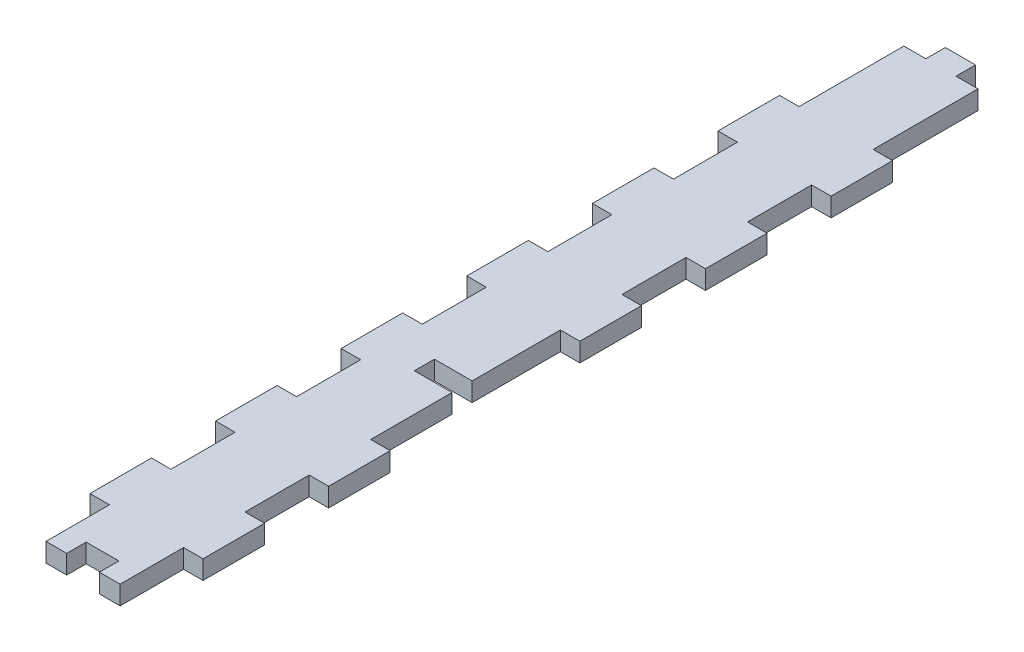
SolidWorks part; units mm, degrees
ref_plane "Front Plane" through (0, 0, 0) normal (0, 0, 1) x (1, 0, 0)
ref_plane "Top Plane" through (0, 0, 0) normal (0, 1, 0) x (1, 0, 0)
ref_plane "Right Plane" through (0, 0, 0) normal (1, 0, 0) x (0, 0, -1)
sketch "Sketch1" plane through (0, 0, 0) normal (0, 1, 0) x (1, 0, 0)
  line L0 (0, 0) -> (0, -139.6944) construction
  line L1 (-9, 0) -> (9, 0)
  line L2 (-9, 0) -> (-9, -139.6944)
  line L3 (-9, -139.6944) -> (9, -139.6944)
  line L4 (9, 0) -> (9, -139.6944)
extrude "Boss-Extrude1" add sketch "Sketch1" against normal up to vertex (3 mm away)
sketch "Sketch2" plane through (0, 0, 0) normal (0, 1, 0) x (1, 0, 0)
  line L0 (6, -3) -> (6, -139.6944) construction
  line L1 (-6, -139.6944) -> (-6, -3) construction
  line L2 (6, -3) -> (-6, -3) construction
  line L3 (-6, -3) -> (-6, 0) construction
  line L4 (9, 0) -> (-9, 0)
  line L5 (9, -139.6944) -> (9, 0)
  line L6 (-9, -139.6944) -> (9, -139.6944)
  line L7 (-9, 0) -> (-9, -139.6944)
  line L8 (9, 0) -> (-9, 0) construction
  line L9 (9, -139.6944) -> (9, 0) construction
  line L10 (-9, -139.6944) -> (9, -139.6944) construction
  line L11 (-9, 0) -> (-9, -139.6944) construction
  line L12 (-6, -3) -> (-9, -3) construction
  line L13 (2.5, 0) -> (9, 0)
  line L14 (9, -39.6944) -> (6, -39.6944)
  line L15 (2.5, -3) -> (2.5, 0)
  line L17 (0, 0) -> (0, -139.6944) construction
  line L18 (9, -49.6944) -> (6, -49.6944)
  line L20 (9, 0) -> (9, -19.6944)
  line L21 (9, -29.6944) -> (6, -29.6944)
  line L22 (6, -19.6944) -> (6, -3)
  line L23 (6, -3) -> (2.5, -3)
  line L24 (9, -19.6944) -> (6, -19.6944)
  line L25 (9, -59.6944) -> (6, -59.6944)
  line L27 (9, -69.6944) -> (6, -69.6944)
  line L29 (9, -79.6944) -> (6, -79.6944) construction
  line L31 (9, -109.6944) -> (6, -109.6944)
  line L33 (9, -119.6944) -> (6, -119.6944)
  line L35 (9, -129.6944) -> (6, -129.6944)
  line L37 (-9, -119.6944) -> (-6, -119.6944)
  line L39 (-9, -129.6944) -> (-6, -129.6944)
  line L41 (-9, -79.6944) -> (-6, -79.6944)
  line L42 (-9, -89.6944) -> (-9, -99.6944)
  line L43 (-9, -109.6944) -> (-6, -109.6944)
  line L44 (-6, -89.6944) -> (-6, -99.6944)
  line L45 (-9, -59.6944) -> (-6, -59.6944)
  line L47 (-9, -69.6944) -> (-6, -69.6944)
  line L49 (-9, -39.6944) -> (-6, -39.6944)
  line L51 (-9, -49.6944) -> (-6, -49.6944)
  line L53 (-9, -29.6944) -> (-6, -29.6944)
  line L54 (-9, 0) -> (-9, -19.6944)
  line L55 (-2.5, 0) -> (-9, 0)
  line L56 (-2.5, -3) -> (-2.5, 0)
  line L57 (-6, -3) -> (-2.5, -3)
  line L58 (-6, -19.6944) -> (-6, -3)
  line L59 (9, -89.6944) -> (6, -89.6944) construction
  line L60 (9, -99.6944) -> (6, -99.6944)
  line L61 (9, -136.6944) -> (-9, -136.6944) construction
  line L62 (-6, -19.6944) -> (-9, -19.6944)
  line L67 (2.5, -136.6944) -> (-2.5, -136.6944)
  line L68 (2.5, -136.6944) -> (2.5, -139.6944)
  line L69 (2.5, -139.6944) -> (-2.5, -139.6944)
  line L70 (-2.5, -136.6944) -> (-2.5, -139.6944)
  line L71 (9, -29.6944) -> (9, -39.6944)
  line L72 (6, -29.6944) -> (6, -39.6944)
  line L73 (-6, -29.6944) -> (-6, -39.6944)
  line L74 (-9, -29.6944) -> (-9, -39.6944)
  line L75 (9, -49.6944) -> (9, -59.6944)
  line L76 (6, -49.6944) -> (6, -59.6944)
  line L77 (-6, -49.6944) -> (-6, -59.6944)
  line L78 (-9, -49.6944) -> (-9, -59.6944)
  line L79 (-6, -99.6944) -> (-9, -99.6944)
  line L80 (-6, -89.6944) -> (-9, -89.6944)
  line L81 (9, -69.6944) -> (9, -99.6944)
  line L82 (6, -69.6944) -> (6, -83.7444)
  line L83 (-6, -69.6944) -> (-6, -79.6944)
  line L84 (-9, -69.6944) -> (-9, -79.6944)
  line L85 (6, -86.7444) -> (6, -99.6944)
  line L86 (9, -109.6944) -> (9, -119.6944)
  line L87 (6, -109.6944) -> (6, -119.6944)
  line L88 (-6, -109.6944) -> (-6, -119.6944)
  line L89 (-9, -109.6944) -> (-9, -119.6944)
  line L90 (-6, -129.6944) -> (-6, -139.6944)
  line L91 (-6, -139.6944) -> (-9, -139.6944)
  line L92 (-9, -139.6944) -> (-9, -129.6944)
  line L93 (6, -129.6944) -> (6, -139.6944)
  line L94 (6, -139.6944) -> (9, -139.6944)
  line L95 (9, -139.6944) -> (9, -129.6944)
  line L96 (-9, -83.7444) -> (9, -83.7444) construction
  line L97 (9, -86.7444) -> (-9, -86.7444) construction
  line L99 (6, -83.7444) -> (0, -83.7444)
  line L101 (6, -86.7444) -> (0, -86.7444)
  line L102 (0, -83.7444) -> (0, -86.7444)
  dimension "D1" = 0
sketch "Sketch4" plane through (0, 0, 0) normal (0, 1, 0) x (1, 0, 0)
  line L0 (5.9, -19.7944) -> (9.1, -19.7944)
  line L1 (9.1, -19.7944) -> (9.1, 0.1)
  line L2 (9.1, 0.1) -> (2.4, 0.1)
  line L3 (2.4, 0.1) -> (2.4, -3.1)
  line L4 (9, -49.6944) -> (6, -49.6944)
  line L5 (6, -49.6944) -> (6, -59.6944)
  line L6 (6, -19.6944) -> (9, -19.6944)
  line L7 (9, -19.6944) -> (9, 0)
  line L8 (9, 0) -> (2.5, 0)
  line L9 (2.5, 0) -> (2.5, -3)
  line L10 (2.5, -3) -> (6, -3)
  line L11 (6, -3) -> (6, -19.6944)
  line L12 (6, -19.6944) -> (9, -19.6944) construction
  line L13 (9, -19.6944) -> (9, 0) construction
  line L14 (9, 0) -> (2.5, 0) construction
  line L15 (2.5, 0) -> (2.5, -3) construction
  line L16 (2.5, -3) -> (6, -3) construction
  line L17 (6, -3) -> (6, -19.6944) construction
  line L18 (6, -59.6944) -> (9, -59.6944)
  line L19 (9, -59.6944) -> (9, -49.6944)
  line L20 (9, -49.6944) -> (6, -49.6944) construction
  line L21 (6, -49.6944) -> (6, -59.6944) construction
  line L22 (6, -59.6944) -> (9, -59.6944) construction
  line L23 (9, -59.6944) -> (9, -49.6944) construction
  line L24 (6, -39.6944) -> (9, -39.6944)
  line L25 (6, -29.6944) -> (6, -39.6944)
  line L26 (9, -29.6944) -> (6, -29.6944)
  line L27 (9, -39.6944) -> (9, -29.6944)
  line L28 (6, -39.6944) -> (9, -39.6944) construction
  line L29 (6, -29.6944) -> (6, -39.6944) construction
  line L30 (9, -29.6944) -> (6, -29.6944) construction
  line L31 (9, -39.6944) -> (9, -29.6944) construction
  line L32 (9, -129.6944) -> (6, -129.6944)
  line L33 (6, -129.6944) -> (6, -139.6944)
  line L34 (6, -139.6944) -> (9, -139.6944)
  line L35 (9, -139.6944) -> (9, -129.6944)
  line L36 (9, -129.6944) -> (6, -129.6944) construction
  line L37 (6, -129.6944) -> (6, -139.6944) construction
  line L38 (6, -139.6944) -> (9, -139.6944) construction
  line L39 (9, -139.6944) -> (9, -129.6944) construction
  line L40 (9, -109.6944) -> (6, -109.6944)
  line L41 (6, -109.6944) -> (6, -119.6944)
  line L42 (6, -119.6944) -> (9, -119.6944)
  line L43 (9, -119.6944) -> (9, -109.6944)
  line L44 (9, -109.6944) -> (6, -109.6944) construction
  line L45 (6, -109.6944) -> (6, -119.6944) construction
  line L46 (6, -119.6944) -> (9, -119.6944) construction
  line L47 (9, -119.6944) -> (9, -109.6944) construction
  line L48 (-9, -59.6944) -> (-6, -59.6944)
  line L49 (-6, -59.6944) -> (-6, -49.6944)
  line L50 (-6, -49.6944) -> (-9, -49.6944)
  line L51 (-9, -49.6944) -> (-9, -59.6944)
  line L52 (-9, -59.6944) -> (-6, -59.6944) construction
  line L53 (-6, -59.6944) -> (-6, -49.6944) construction
  line L54 (-6, -49.6944) -> (-9, -49.6944) construction
  line L55 (-9, -49.6944) -> (-9, -59.6944) construction
  line L56 (-6, -109.6944) -> (-9, -109.6944)
  line L57 (-6, -119.6944) -> (-6, -109.6944)
  line L58 (-9, -119.6944) -> (-6, -119.6944)
  line L59 (-9, -109.6944) -> (-9, -119.6944)
  line L60 (-6, -109.6944) -> (-9, -109.6944) construction
  line L61 (-6, -119.6944) -> (-6, -109.6944) construction
  line L62 (-9, -119.6944) -> (-6, -119.6944) construction
  line L63 (-9, -109.6944) -> (-9, -119.6944) construction
  line L64 (-9, -79.6944) -> (-6, -79.6944)
  line L65 (-6, -79.6944) -> (-6, -69.6944)
  line L66 (-6, -69.6944) -> (-9, -69.6944)
  line L67 (-9, -69.6944) -> (-9, -79.6944)
  line L68 (-9, -79.6944) -> (-6, -79.6944) construction
  line L69 (-6, -79.6944) -> (-6, -69.6944) construction
  line L70 (-6, -69.6944) -> (-9, -69.6944) construction
  line L71 (-9, -69.6944) -> (-9, -79.6944) construction
  line L72 (-6, -129.6944) -> (-9, -129.6944)
  line L73 (-6, -139.6944) -> (-6, -129.6944)
  line L74 (-9, -139.6944) -> (-6, -139.6944)
  line L75 (-9, -129.6944) -> (-9, -139.6944)
  line L76 (-6, -129.6944) -> (-9, -129.6944) construction
  line L77 (-6, -139.6944) -> (-6, -129.6944) construction
  line L78 (-9, -139.6944) -> (-6, -139.6944) construction
  line L79 (-9, -129.6944) -> (-9, -139.6944) construction
  line L80 (-6, -39.6944) -> (-6, -29.6944)
  line L81 (-9, -39.6944) -> (-6, -39.6944)
  line L82 (-9, -29.6944) -> (-9, -39.6944)
  line L83 (-6, -29.6944) -> (-9, -29.6944)
  line L84 (-6, -39.6944) -> (-6, -29.6944) construction
  line L85 (-9, -39.6944) -> (-6, -39.6944) construction
  line L86 (-9, -29.6944) -> (-9, -39.6944) construction
  line L87 (-6, -29.6944) -> (-9, -29.6944) construction
  line L88 (-9, -89.6944) -> (-9, -99.6944)
  line L89 (-9, -99.6944) -> (-6, -99.6944)
  line L90 (-6, -99.6944) -> (-6, -89.6944)
  line L91 (-6, -89.6944) -> (-9, -89.6944)
  line L92 (-9, -89.6944) -> (-9, -99.6944) construction
  line L93 (-9, -99.6944) -> (-6, -99.6944) construction
  line L94 (-6, -99.6944) -> (-6, -89.6944) construction
  line L95 (-6, -89.6944) -> (-9, -89.6944) construction
  line L96 (2.5, -136.6944) -> (-2.5, -136.6944)
  line L97 (-2.5, -136.6944) -> (-2.5, -139.6944)
  line L98 (-2.5, -139.6944) -> (2.5, -139.6944)
  line L99 (2.5, -139.6944) -> (2.5, -136.6944)
  line L100 (6, -83.7444) -> (0, -83.7444)
  line L101 (6, -69.6944) -> (6, -83.7444)
  line L102 (9, -69.6944) -> (6, -69.6944)
  line L103 (9, -99.6944) -> (9, -69.6944)
  line L104 (6, -99.6944) -> (9, -99.6944)
  line L105 (6, -86.7444) -> (6, -99.6944)
  line L106 (0, -86.7444) -> (6, -86.7444)
  line L107 (0, -83.7444) -> (0, -86.7444)
  line L108 (6, -83.7444) -> (0, -83.7444) construction
  line L109 (6, -69.6944) -> (6, -83.7444) construction
  line L110 (9, -69.6944) -> (6, -69.6944) construction
  line L111 (9, -99.6944) -> (9, -69.6944) construction
  line L112 (6, -99.6944) -> (9, -99.6944) construction
  line L113 (6, -86.7444) -> (6, -99.6944) construction
  line L114 (0, -86.7444) -> (6, -86.7444) construction
  line L115 (0, -83.7444) -> (0, -86.7444) construction
  line L116 (2.5, -136.6944) -> (-2.5, -136.6944) construction
  line L117 (-2.5, -136.6944) -> (-2.5, -139.6944) construction
  line L118 (-2.5, -139.6944) -> (2.5, -139.6944) construction
  line L119 (2.5, -139.6944) -> (2.5, -136.6944) construction
  line L120 (2.4, -3.1) -> (5.9, -3.1)
  line L121 (5.9, -3.1) -> (5.9, -19.7944)
  line L122 (-9, 0) -> (-9, -19.6944)
  line L123 (-2.5, 0) -> (-9, 0)
  line L124 (-2.5, -3) -> (-2.5, 0)
  line L125 (-6, -3) -> (-2.5, -3)
  line L126 (-6, -19.6944) -> (-6, -3)
  line L127 (-9, -19.6944) -> (-6, -19.6944)
  line L128 (-9, 0) -> (-9, -19.6944) construction
  line L129 (-2.5, 0) -> (-9, 0) construction
  line L130 (-2.5, -3) -> (-2.5, 0) construction
  line L131 (-6, -3) -> (-2.5, -3) construction
  line L132 (-6, -19.6944) -> (-6, -3) construction
  line L133 (-9, -19.6944) -> (-6, -19.6944) construction
  line L134 (9.1, -49.5944) -> (5.9, -49.5944)
  line L135 (5.9, -49.5944) -> (5.9, -59.7944)
  line L136 (5.9, -59.7944) -> (9.1, -59.7944)
  line L137 (9.1, -59.7944) -> (9.1, -49.5944)
  line L138 (5.9, -39.7944) -> (9.1, -39.7944)
  line L139 (9.1, -39.7944) -> (9.1, -29.5944)
  line L140 (9.1, -29.5944) -> (5.9, -29.5944)
  line L141 (5.9, -29.5944) -> (5.9, -39.7944)
  line L142 (9.1, -129.5944) -> (5.9, -129.5944)
  line L143 (5.9, -129.5944) -> (5.9, -139.7944)
  line L144 (5.9, -139.7944) -> (9.1, -139.7944)
  line L145 (9.1, -139.7944) -> (9.1, -129.5944)
  line L146 (9.1, -109.5944) -> (5.9, -109.5944)
  line L147 (5.9, -109.5944) -> (5.9, -119.7944)
  line L148 (5.9, -119.7944) -> (9.1, -119.7944)
  line L149 (9.1, -119.7944) -> (9.1, -109.5944)
  line L150 (-9.1, -59.7944) -> (-5.9, -59.7944)
  line L151 (-5.9, -59.7944) -> (-5.9, -49.5944)
  line L152 (-5.9, -49.5944) -> (-9.1, -49.5944)
  line L153 (-9.1, -49.5944) -> (-9.1, -59.7944)
  line L154 (-5.9, -109.5944) -> (-9.1, -109.5944)
  line L155 (-9.1, -109.5944) -> (-9.1, -119.7944)
  line L156 (-9.1, -119.7944) -> (-5.9, -119.7944)
  line L157 (-5.9, -119.7944) -> (-5.9, -109.5944)
  line L158 (-9.1, -79.7944) -> (-5.9, -79.7944)
  line L159 (-5.9, -79.7944) -> (-5.9, -69.5944)
  line L160 (-5.9, -69.5944) -> (-9.1, -69.5944)
  line L161 (-9.1, -69.5944) -> (-9.1, -79.7944)
  line L162 (-5.9, -129.5944) -> (-9.1, -129.5944)
  line L163 (-9.1, -129.5944) -> (-9.1, -139.7944)
  line L164 (-9.1, -139.7944) -> (-5.9, -139.7944)
  line L165 (-5.9, -139.7944) -> (-5.9, -129.5944)
  line L166 (-5.9, -39.7944) -> (-5.9, -29.5944)
  line L167 (-5.9, -29.5944) -> (-9.1, -29.5944)
  line L168 (-9.1, -29.5944) -> (-9.1, -39.7944)
  line L169 (-9.1, -39.7944) -> (-5.9, -39.7944)
  line L170 (-9.1, -89.5944) -> (-9.1, -99.7944)
  line L171 (-9.1, -99.7944) -> (-5.9, -99.7944)
  line L172 (-5.9, -99.7944) -> (-5.9, -89.5944)
  line L173 (-5.9, -89.5944) -> (-9.1, -89.5944)
  line L174 (5.9, -83.6444) -> (-0.1, -83.6444)
  line L175 (-0.1, -83.6444) -> (-0.1, -86.8444)
  line L176 (-0.1, -86.8444) -> (5.9, -86.8444)
  line L177 (5.9, -86.8444) -> (5.9, -99.7944)
  line L178 (5.9, -99.7944) -> (9.1, -99.7944)
  line L179 (9.1, -99.7944) -> (9.1, -69.5944)
  line L180 (9.1, -69.5944) -> (5.9, -69.5944)
  line L181 (5.9, -69.5944) -> (5.9, -83.6444)
  line L182 (2.6, -136.5944) -> (-2.6, -136.5944)
  line L183 (-2.6, -136.5944) -> (-2.6, -139.7944)
  line L184 (-2.6, -139.7944) -> (2.6, -139.7944)
  line L185 (2.6, -139.7944) -> (2.6, -136.5944)
  line L186 (-9.1, 0.1) -> (-9.1, -19.7944)
  line L187 (-9.1, -19.7944) -> (-5.9, -19.7944)
  line L188 (-5.9, -19.7944) -> (-5.9, -3.1)
  line L189 (-5.9, -3.1) -> (-2.4, -3.1)
  line L190 (-2.4, -3.1) -> (-2.4, 0.1)
  line L191 (-2.4, 0.1) -> (-9.1, 0.1)
  dimension "D1" = 0
  dimension "D2" = 0
  dimension "D3" = 0
  dimension "D4" = 0
  dimension "D5" = 0
  dimension "D6" = 0
  dimension "D7" = 0
  dimension "D8" = 0
  dimension "D9" = 0
  dimension "D10" = 0
  dimension "D11" = 0
  dimension "D12" = 0
  dimension "D13" = 0
  dimension "D14" = 0
  dimension "D15" = 0.1
extrude "Cut-Extrude2" cut sketch "Sketch4" against normal through all
